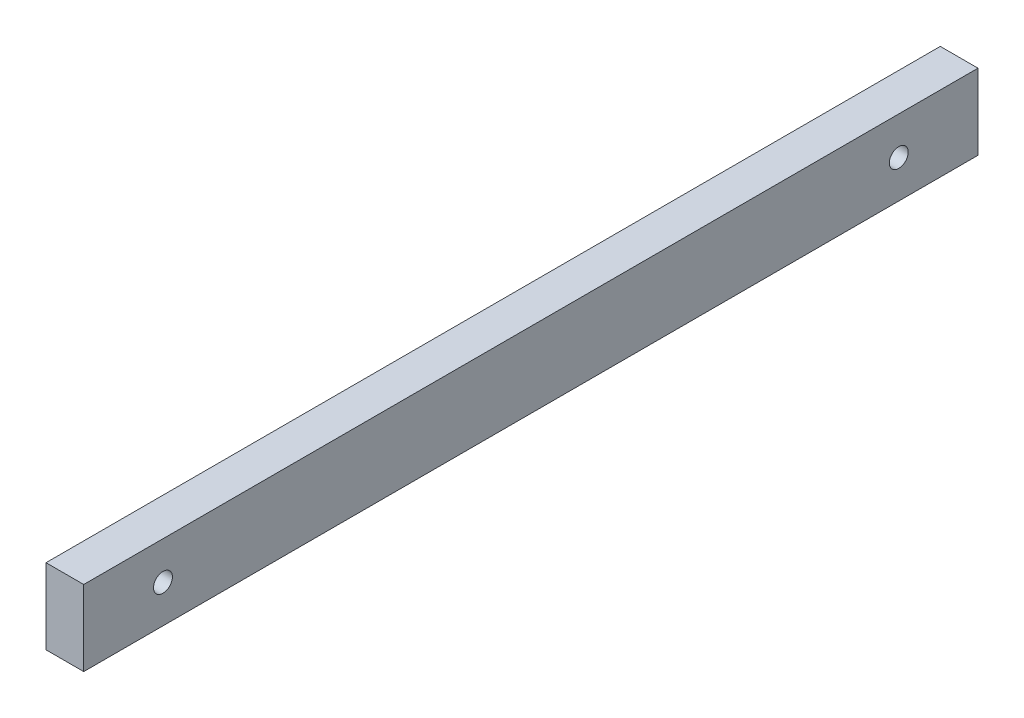
SolidWorks part; units mm, degrees
ref_plane "Front Plane" through (0, 0, 0) normal (0, 0, 1) x (1, 0, 0)
ref_plane "Top Plane" through (0, 0, 0) normal (0, 1, 0) x (1, 0, 0)
ref_plane "Right Plane" through (0, 0, 0) normal (1, 0, 0) x (0, 0, -1)
sketch "Sketch1" plane through (0, 0, 0) normal (0, 1, 0) x (1, 0, 0)
  line L1 (-5, 118.5) -> (5, 118.5)
  line L2 (-5, 118.5) -> (-5, -118.5)
  line L3 (-5, -118.5) -> (5, -118.5)
  line L4 (5, 118.5) -> (5, -118.5)
  line L5 (-5, 118.5) -> (5, -118.5) construction
  line L6 (-5, -118.5) -> (5, 118.5) construction
  point P0 (0, 0)
  dimension "D1" = 10
  dimension "D2" = 237
extrude "Boss-Extrude2" add sketch "Sketch1" along normal blind 20
sketch "Sketch2" plane through (0, 0, 0) normal (1, 0, 0) x (0, 0, -1)
sketch "Sketch4" plane through (5, 0, 0) normal (1, 0, 0) x (0, 0, -1)
  line L0 (-97.5, 20) -> (-97.5, 0) construction
  line L1 (-118.5, 20) -> (118.5, 20) construction
  line L2 (-118.5, 0) -> (118.5, 0) construction
  line L3 (-118.5, 20) -> (-118.5, 0) construction
  line L4 (97.5, 20) -> (97.5, 0) construction
  line L5 (118.5, 20) -> (118.5, 0) construction
  circle A0 centre (-97.5, 10) radius 2.5
  circle A1 centre (97.5, 10) radius 2.5
  point P8 (-118.5, 10)
  point P15 (118.5, 10)
  dimension "D1" = 5
  dimension "D3" = 5
  dimension "D2" = 21
  dimension "D4" = 21
extrude "Cut-Extrude2" cut sketch "Sketch4" against normal blind 10
